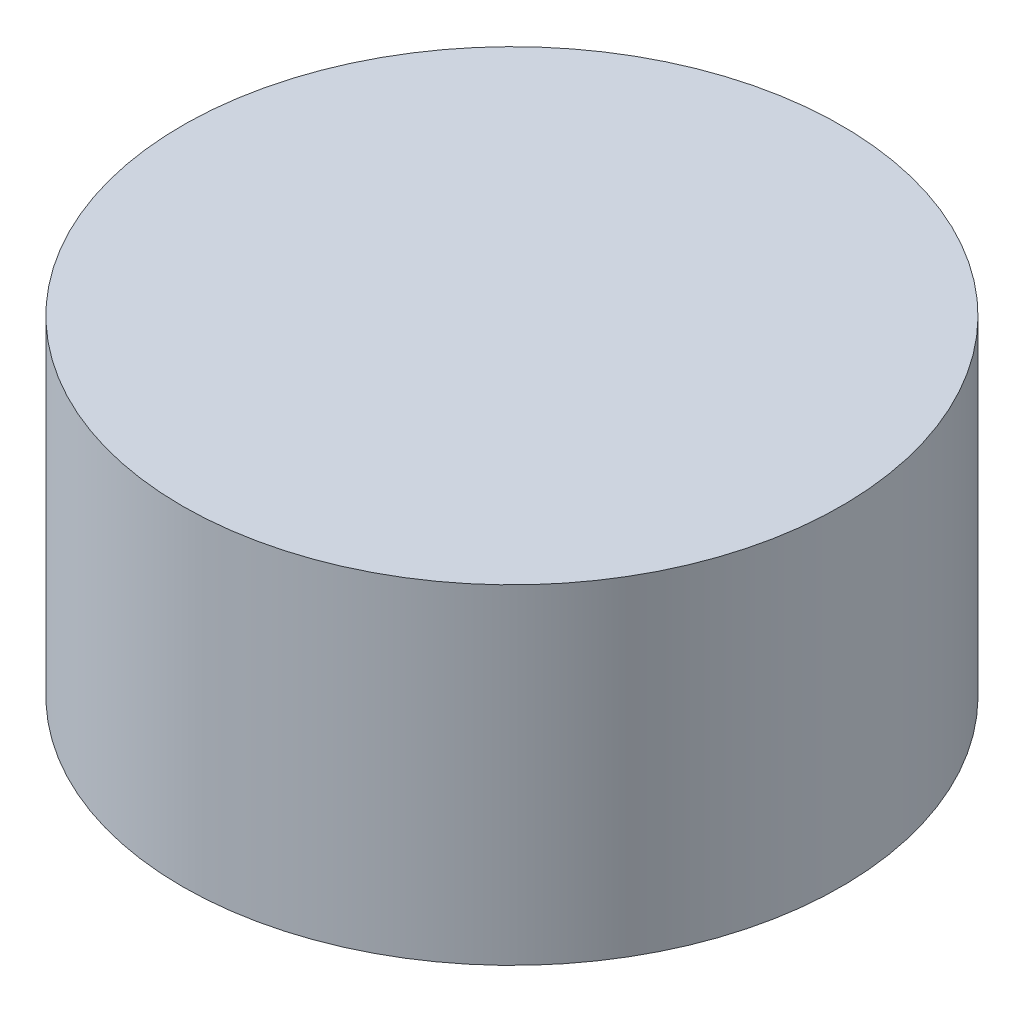
SolidWorks part; units mm, degrees
ref_plane "Front Plane" through (0, 0, 0) normal (0, 0, 1) x (1, 0, 0)
ref_plane "Top Plane" through (0, 0, 0) normal (0, 1, 0) x (1, 0, 0)
ref_plane "Right Plane" through (0, 0, 0) normal (1, 0, 0) x (0, 0, -1)
sketch "Sketch1" plane through (0, 0, 0) normal (0, 1, 0) x (1, 0, 0)
  circle A0 centre (0, 0) radius 1
  dimension "D1" = 2
extrude "Boss-Extrude1" add sketch "Sketch1" along normal blind 1
